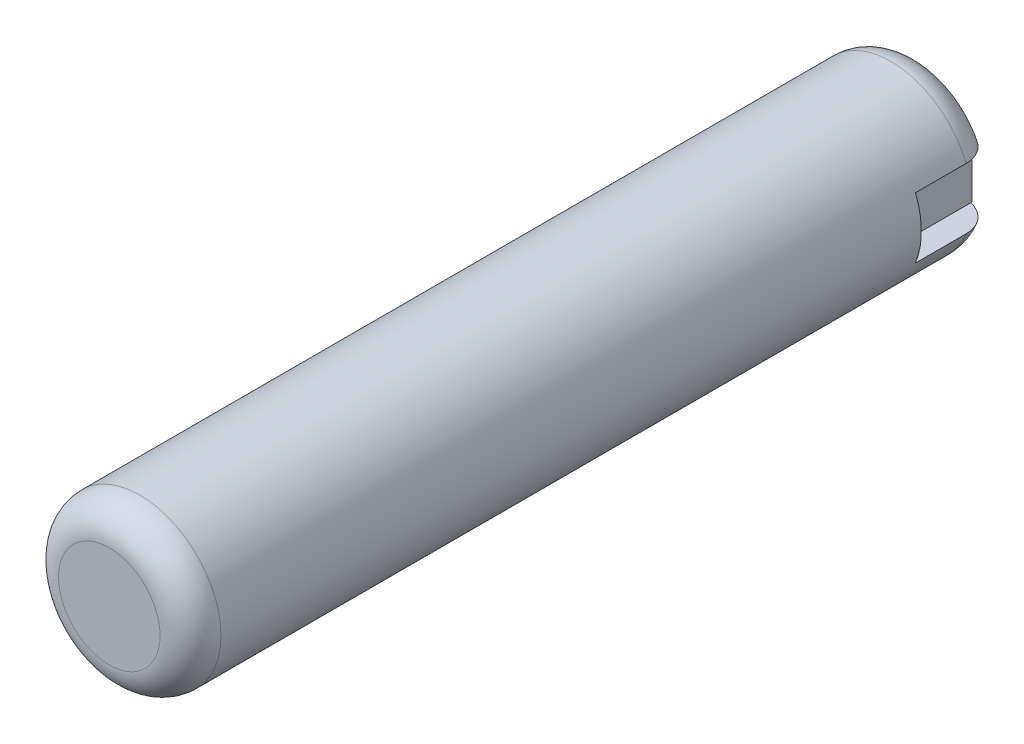
SolidWorks part; units mm, degrees
material "Stub"
ref_plane "Face" through (0, 0, 0) normal (0, 0, 1) x (1, 0, 0)
ref_plane "Dessus" through (0, 0, 0) normal (0, 1, 0) x (1, 0, 0)
ref_plane "Droite" through (0, 0, 0) normal (1, 0, 0) x (0, 0, -1)
sketch "Esquisse1" plane through (0, 0, 0) normal (0, 0, 1) x (1, 0, 0)
  circle A0 centre (0, 0) radius 4
  dimension "D1" = 8
extrude "Boss.-Extru.1" add sketch "Esquisse1" along normal mid plane 40
fillet "Congé1" radius 1.5 2 edges at (4, 0, -20) (4, 0, 20)
sketch "Esquisse2" plane through (0, 0, 0) normal (1, 0, 0) x (0, 0, -1)
  line L0 (20, -2.5) -> (20, 2.5) construction
  line L1 (20, 1.5) -> (16, 1.5)
  line L2 (20, 1.5) -> (20, -1.5)
  line L3 (20, -1.5) -> (16, -1.5)
  line L4 (16, 1.5) -> (16, -1.5)
  line L5 (0, 0) -> (16, 0) construction
  dimension "D1" = 3
  dimension "D2" = 4
extrude "Enlèv. mat.-Extru.1" cut sketch "Esquisse2" against normal mid plane 10
sketch "Esquisse3" plane through (0, 0, -16) normal (0, 0, -1) x (-1, 0, 0)
  line L0 (-3.7081, 1.5) -> (-2, 1.5) construction
  line L1 (-2.5, 1.5) -> (2.5, 1.5)
  line L2 (-2.5, 1.5) -> (-2.5, -1.5)
  line L3 (-2.5, -1.5) -> (2.5, -1.5)
  line L4 (2.5, 1.5) -> (2.5, -1.5)
  line L5 (3.7081, -1.5) -> (2, -1.5) construction
  line L6 (-2.5, 1.5) -> (2.5, -1.5) construction
  dimension "D1" = 5
extrude "Boss.-Extru.2" add sketch "Esquisse3" along direction (0, 0, 1) on the side of the normal up to surface (4 mm away) separate body
